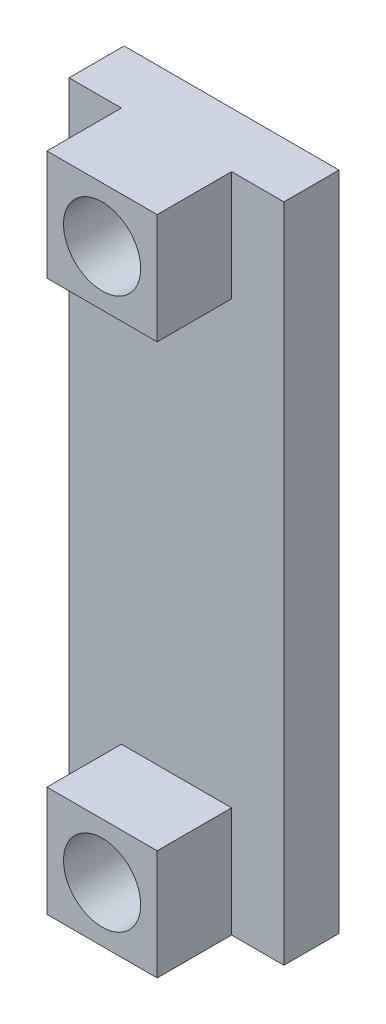
SolidWorks part; units mm, degrees
material "Copper"
ref_plane "Front Plane" through (0, 0, 0) normal (0, 0, 1) x (1, 0, 0)
ref_plane "Top Plane" through (0, 0, 0) normal (0, 1, 0) x (1, 0, 0)
ref_plane "Right Plane" through (0, 0, 0) normal (1, 0, 0) x (0, 0, -1)
sketch "Sketch1" plane through (0, 0, 0) normal (0, 0, 1) x (1, 0, 0)
  line L1 (0, 0) -> (-9.906, 0)
  line L2 (0, 0) -> (0, -30.48)
  line L3 (0, -30.48) -> (-9.906, -30.48)
  line L4 (-9.906, 0) -> (-9.906, -30.48)
  dimension "D1" = 9.906
  dimension "D2" = 30.48
extrude "Boss-Extrude1" add sketch "Sketch1" along normal blind 2.54
sketch "Sketch2" plane through (0, 0, 2.54) normal (0, 0, 1) x (1, 0, 0)
  line L0 (0, 0) -> (-9.906, 0) construction
  line L1 (-7.493, 0) -> (-2.413, 0)
  line L2 (-7.493, 0) -> (-7.493, -5.08)
  line L3 (-7.493, -5.08) -> (-2.413, -5.08)
  line L4 (-2.413, 0) -> (-2.413, -5.08)
  line L5 (-9.906, -30.48) -> (0, -30.48) construction
  line L6 (-7.493, -30.48) -> (-2.413, -30.48)
  line L7 (-7.493, -30.48) -> (-7.493, -25.4)
  line L8 (-7.493, -25.4) -> (-2.413, -25.4)
  line L9 (-2.413, -30.48) -> (-2.413, -25.4)
  line L10 (-9.906, 0) -> (-9.906, -30.48) construction
  dimension "D1" = 5.08
  dimension "D2" = 5.08
  dimension "D3" = 5.08
  dimension "D4" = 2.413
  dimension "D5" = 2.413
  dimension "D6" = 5.08
extrude "Boss-Extrude2" add sketch "Sketch2" along normal blind 3.429
sketch "Sketch3" plane through (0, 0, 5.969) normal (0, 0, 1) x (1, 0, 0)
  line L0 (-2.413, -30.48) -> (-2.413, -25.4) construction
  line L1 (-2.413, -25.4) -> (-7.493, -25.4) construction
  line L2 (-7.493, -5.08) -> (-2.413, -5.08) construction
  line L3 (-2.413, -5.08) -> (-2.413, 0) construction
  circle A0 centre (-4.953, -27.94) radius 1.778
  circle A1 centre (-4.953, -2.54) radius 1.778
  dimension "D1" = 3.556
  dimension "D6" = 3.556
  dimension "D2" = 2.54
  dimension "D3" = 2.54
  dimension "D4" = 2.54
  dimension "D5" = 2.54
extrude "Cut-Extrude1" cut sketch "Sketch3" against normal blind 12.7
